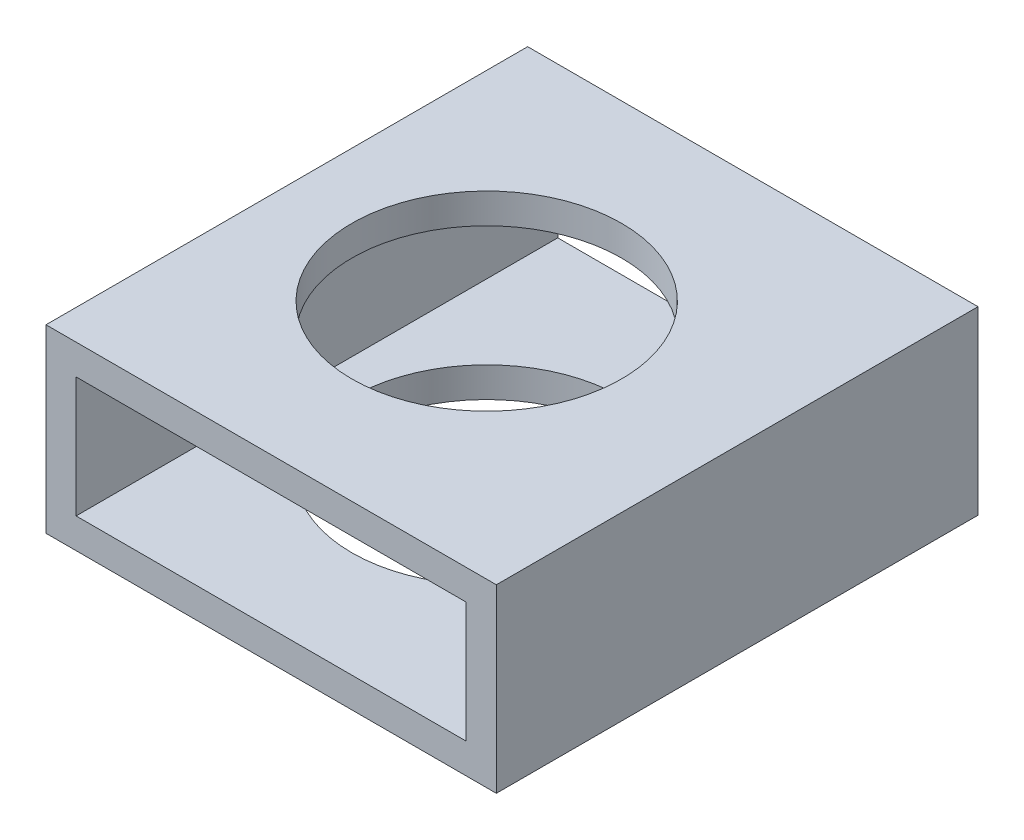
SolidWorks part; units mm, degrees
ref_plane "Front" through (0, 0, 0) normal (0, 0, 1) x (1, 0, 0)
ref_plane "Top" through (0, 0, 0) normal (0, 1, 0) x (1, 0, 0)
ref_plane "Right" through (0, 0, 0) normal (1, 0, 0) x (0, 0, -1)
sketch "Sketch1" plane through (0, 0, 0) normal (0, 0, 1) x (1, 0, 0)
  line L1 (-54.2623, 21.1125) -> (-6.7643, 21.1125)
  line L2 (-54.2623, 21.1125) -> (-54.2623, 2.0625)
  line L3 (-54.2623, 2.0625) -> (-6.7643, 2.0625)
  line L4 (-6.7643, 21.1125) -> (-6.7643, 2.0625)
  dimension "D1" = 47.498
  dimension "D2" = 19.05
extrude "Boss-Extrude1" add sketch "Sketch1" along normal blind 50.8
sketch "Sketch2" plane through (0, 0, 0) normal (0, 0, -1) x (-1, 0, 0)
  line L8 (51.0873, 5.2375) -> (51.0873, 17.9375)
  line L9 (51.0873, 17.9375) -> (9.9393, 17.9375)
  line L10 (9.9393, 17.9375) -> (9.9393, 5.2375)
  line L11 (9.9393, 5.2375) -> (51.0873, 5.2375)
  line L12 (51.0873, 5.2375) -> (51.0873, 17.9375)
  line L13 (51.0873, 17.9375) -> (9.9393, 17.9375)
  line L14 (9.9393, 17.9375) -> (9.9393, 5.2375)
  line L15 (9.9393, 5.2375) -> (51.0873, 5.2375)
  dimension "D1" = 3.175
extrude "Cut-Extrude1" cut sketch "Sketch2" against normal through all
sketch "Sketch5" plane through (0, 21.1125, 0) normal (0, 1, 0) x (1, 0, 0)
  line L1 (-6.7643, -50.8) -> (-6.7643, 0) construction
  line L2 (-6.7643, -25.4) -> (-33.1803, -25.4)
  circle A0 centre (-33.1803, -25.4) radius 14.224
extrude "Cut-Extrude2" cut sketch "Sketch5" against normal through all contours A0
